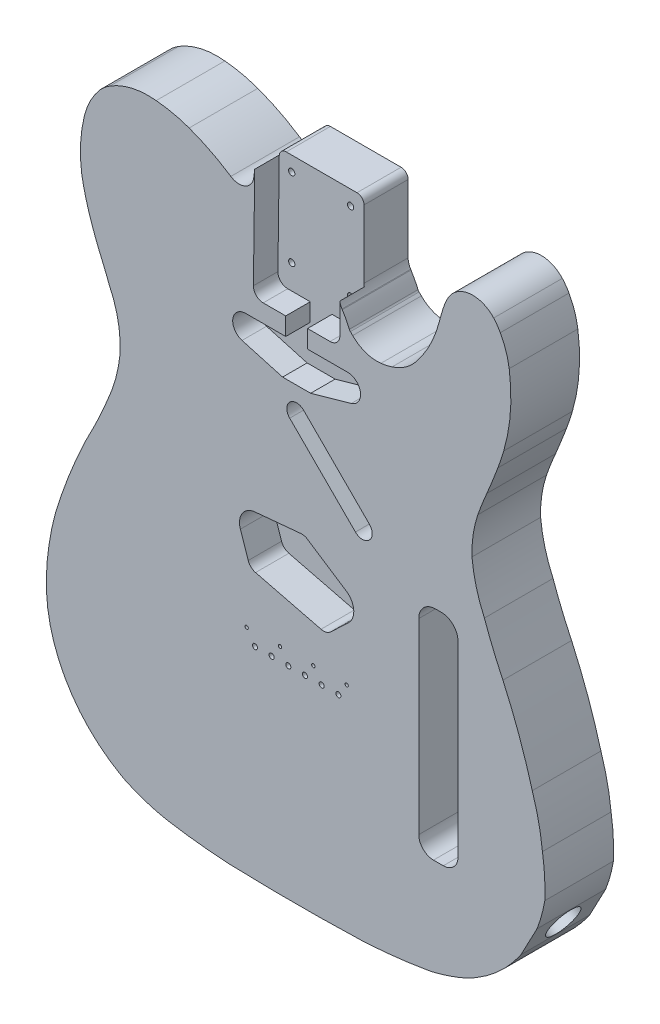
SolidWorks part; units mm, degrees
material "Teak"
ref_plane "Front Plane" through (0, 0, 0) normal (0, 0, 1) x (1, 0, 0)
ref_plane "Top Plane" through (0, 0, 0) normal (0, 1, 0) x (1, 0, 0)
ref_plane "Right Plane" through (0, 0, 0) normal (1, 0, 0) x (0, 0, -1)
sketch "Sketch1" plane through (0, 0, 0) normal (0, 0, 1) x (1, 0, 0)
  line L0 (255.3675, -212.0656) -> (264.4462, -212.0656)
  line L1 (264.4462, -212.0656) -> (273.5248, -212.0656)
  line L2 (254.4921, -211.9425) -> (229.09, -204.656)
  line L3 (274.4003, -211.9425) -> (299.8024, -204.656)
  line L4 (264.4462, -197.0288) -> (264.4462, -188.6259)
  line L5 (292.1992, -149.0184) -> (292.1992, -105.0808)
  line L6 (353.0408, -434.0524) -> (359.3908, -434.0524)
  line L7 (354.3108, -292.5744) -> (358.1208, -292.5744)
  line L8 (368.9158, -303.3694) -> (368.9158, -424.5274)
  line L9 (343.5158, -303.3694) -> (343.5158, -424.5274)
  line L10 (231.3871, -188.3166) -> (257.385, -188.3166)
  line L11 (271.5074, -188.3166) -> (297.5053, -188.3166)
  line L12 (292.2083, -154.6088) -> (292.4426, -170.3149)
  line L13 (237.3236, -111.7284) -> (236.4498, -170.3149)
  line L14 (261.2712, -222.8223) -> (261.2712, -212.0656) construction
  line L15 (267.6212, -222.5163) -> (267.6212, -212.0656) construction
  line L16 (355.5808, -417.0887) -> (440.1841, -462.3756) construction
  line L17 (409.7299, -458.6842) -> (420.0941, -439.0232)
  line L26 (233.0908, -326.0407) -> (228.0254, -311.007)
  line L27 (280.249, -340.996) -> (237.8411, -330.4226)
  line L28 (286.5004, -339.3572) -> (298.0308, -328.4613)
  line L29 (271.5011, -294.9508) -> (296.5271, -311.3952)
  line L30 (267.182, -293.874) -> (237.3652, -296.6444)
  line L31 (292.2083, -154.6088) -> (293.7952, -154.6089)
  line L32 (237.3236, -111.7284) -> (236.159, -111.7284)
  line L33 (264.4462, -533.3397) -> (264.4462, -35.9424) construction
  line L34 (264.446, -176.7596) -> (264.446, -168.3324)
  line L35 (242.7991, -176.7596) -> (257.385, -176.7596)
  line L36 (271.5074, -176.7596) -> (286.0933, -176.7596)
  line L37 (271.5074, -188.3166) -> (271.5074, -176.7596)
  line L38 (257.385, -188.3166) -> (257.385, -176.7596)
  line L39 (311.5028, -266.3979) -> (268.9363, -223.8315)
  line L40 (302.5225, -275.3781) -> (259.9561, -232.8117)
  line L41 (287.6272, -100.5088) -> (241.8598, -100.5088)
  line L42 (236.7013, -109.5293) -> (237.3226, -104.5183)
  line L45 (368.921, -411.631) -> (420.0941, -439.0232) construction
  line L46 (362.6555, -433.4859) -> (409.7299, -458.6842) construction
  line L47 (300.9797, -323.698) -> (343.5158, -323.698) construction
  line L48 (300.9797, -317.348) -> (343.5158, -317.348) construction
  line L49 (343.5158, -311.8813) -> (308.6561, -277.0216) construction
  line L50 (343.5158, -302.901) -> (313.1462, -272.5315) construction
  arc A0 (298.5861, -163.6364) -> (299.2711, -164.6283) centre (301.4937, -162.3609) ccw
  arc A1 (300.7364, -166.0922) -> (299.2711, -164.6283) centre (222.8934, -242.5472) ccw
  arc A2 (300.7364, -166.0922) -> (319.0259, -172.5122) centre (316.4123, -150.6962) ccw
  arc A3 (319.0259, -172.5122) -> (326.2352, -170.944) centre (314.4164, -133.9661) ccw
  arc A4 (326.2352, -170.944) -> (341.6924, -160.3725) centre (316.2829, -139.806) ccw
  arc A5 (341.6924, -160.3725) -> (356.9315, -129.8398) centre (280.2373, -110.6305) ccw
  arc A6 (360.2177, -118.9602) -> (356.9315, -129.8398) centre (472.2447, -158.7341) ccw
  arc A7 (363.6913, -112.2691) -> (360.2177, -118.9602) centre (386.4375, -128.3247) ccw
  arc A8 (392.0008, -110.6336) -> (363.6913, -112.2691) centre (378.4982, -122.7399) ccw
  arc A9 (396.3203, -116.7099) -> (392.0008, -110.6336) centre (367.666, -132.5065) ccw
  arc A10 (402.0691, -133.9701) -> (396.3203, -116.7099) centre (352.5181, -140.8862) ccw
  arc A11 (398.5108, -181.9349) -> (402.0691, -133.9701) centre (289.2584, -149.7157) ccw
  arc A12 (394.7117, -193.3187) -> (398.5108, -181.9349) centre (237.0194, -134.3662) ccw
  arc A13 (387.6043, -211.1738) -> (394.7117, -193.3187) centre (-23.048, -37.3677) ccw
  arc A14 (387.6043, -211.1738) -> (381.762, -226.053) centre (576.8456, -294.0659) ccw
  circle A15 centre (378.0352, -293.8788) radius 0.889
  arc A16 (425.1222, -420.753) -> (420.0941, -439.0232) centre (331.2243, -404.7385) cw
  arc A17 (380.6123, -486.1629) -> (409.7299, -458.6842) centre (333.4551, -407.0266) ccw
  arc A33 (368.9158, -303.3694) -> (358.1208, -292.5744) centre (358.1208, -303.3694) ccw
  arc A34 (354.3108, -292.5744) -> (343.5158, -303.3694) centre (354.3108, -303.3694) ccw
  arc A35 (231.3871, -188.3166) -> (229.09, -204.656) centre (231.3871, -196.6478) ccw
  arc A36 (299.8024, -204.656) -> (297.5053, -188.3166) centre (297.5053, -196.6478) ccw
  arc A37 (273.5248, -212.0656) -> (274.4003, -211.9425) centre (273.5248, -208.8906) ccw
  arc A38 (254.4921, -211.9425) -> (255.3675, -212.0656) centre (255.3675, -208.8906) ccw
  circle A39 centre (300.6412, -197.0288) radius 2.3813
  circle A40 centre (228.2512, -197.0288) radius 2.3813
  circle A41 centre (190.7346, -293.8788) radius 0.889
  circle A45 centre (216.6438, -195.7754) radius 0.9906
  circle A46 centre (237.8426, -363.958) radius 0.9906
  arc A47 (369.9797, -491.4239) -> (380.6123, -486.1629) centre (341.6053, -420.7038) ccw
  circle A49 centre (361.0363, -437.4278) radius 0.9906
  circle A50 centre (375.8404, -153.7439) radius 0.9906
  arc A51 (292.1992, -105.0808) -> (287.6272, -100.5088) centre (287.6272, -105.0808) ccw
  arc A52 (359.3908, -434.0524) -> (368.9158, -424.5274) centre (359.3908, -424.5274) ccw
  arc A53 (343.5158, -424.5274) -> (353.0408, -434.0524) centre (353.0408, -424.5274) ccw
  circle A55 centre (356.2158, -289.002) radius 0.8255
  circle A56 centre (356.2158, -437.6248) radius 0.8255
  circle A57 centre (264.4462, -249.0804) radius 1.5875
  circle A58 centre (264.4462, -477.6804) radius 1.5875
  arc A59 (286.0933, -176.7596) -> (292.4426, -170.3149) centre (286.0933, -170.4096) ccw
  arc A60 (236.4498, -170.3149) -> (242.7991, -176.7596) centre (242.7991, -170.4096) ccw
  circle A61 centre (296.8434, -363.9576) radius 1.0795
  circle A62 centre (275.2536, -363.9576) radius 1.0795
  circle A63 centre (253.664, -363.9576) radius 1.0795
  circle A64 centre (232.0734, -363.9576) radius 1.0795
  circle A65 centre (291.4462, -372.0852) radius 1.651
  circle A66 centre (280.6516, -372.0852) radius 1.651
  circle A67 centre (269.8566, -372.0852) radius 1.651
  circle A68 centre (259.061, -372.0852) radius 1.651
  circle A69 centre (248.2654, -372.0852) radius 1.651
  circle A70 centre (237.4714, -372.0852) radius 1.651
  circle A91 centre (378.3902, -122.9872) radius 0.889
  circle A92 centre (324.0598, -293.8788) radius 0.889
  circle A93 centre (228.8868, -140.5904) radius 0.889
  arc A94 (237.3652, -296.6444) -> (228.0254, -311.007) centre (238.3756, -307.5196) ccw
  arc A95 (233.0908, -326.0407) -> (237.8411, -330.4226) centre (239.4695, -323.8915) ccw
  arc A96 (280.249, -340.996) -> (286.5004, -339.3572) centre (281.8774, -334.465) ccw
  arc A97 (298.0308, -328.4613) -> (296.5271, -311.3952) centre (290.5293, -320.523) ccw
  arc A98 (271.5011, -294.9508) -> (267.182, -293.874) centre (267.8047, -300.5761) ccw
  arc A99 (268.9363, -223.8315) -> (259.9561, -232.8117) centre (264.4462, -228.3216) ccw
  arc A100 (302.5225, -275.3781) -> (311.5028, -275.3781) centre (307.0126, -270.888) ccw
  arc A101 (311.5028, -275.3781) -> (311.5028, -266.3979) centre (307.0126, -270.888) ccw
  circle A102 centre (245.3978, -160.8336) radius 2.032
  circle A103 centre (283.4978, -160.8336) radius 2.032
  circle A104 centre (283.4978, -110.0336) radius 2.032
  circle A105 centre (245.3978, -110.0336) radius 2.032
  arc A106 (241.8598, -100.5088) -> (237.3226, -104.5183) centre (241.8598, -105.0808) ccw
  arc A107 (292.1992, -149.0184) -> (293.7952, -154.6089) centre (302.5829, -149.077) ccw
  arc A108 (293.7952, -154.6089) -> (294.036, -154.9688) centre (302.7937, -148.8489) ccw
  arc A109 (298.5861, -163.6364) -> (294.036, -154.9688) centre (234.5218, -191.7393) ccw
  arc A110 (381.762, -226.053) -> (377.952, -251.638) centre (450.886, -249.4228) ccw
  arc A111 (377.952, -251.638) -> (386, -281.868) centre (472.8009, -242.5731) ccw
  arc A112 (386, -281.868) -> (398, -310.6852) centre (672.9207, -179.2964) ccw
  arc A113 (417, -363.1361) -> (398, -310.6852) centre (74.1269, -457.6731) ccw
  arc A114 (423.6009, -393.9961) -> (417, -363.1361) centre (272.0204, -410.283) ccw
  arc A115 (425.1222, -420.753) -> (423.6009, -393.9961) centre (285.4631, -415.2715) ccw
  arc A116 (353.3461, -496.801) -> (369.9797, -491.4239) centre (322.6987, -373.581) ccw
  arc A117 (307.8756, -502.3376) -> (349.8373, -497.5433) centre (288.5477, -147.1431) ccw
  arc A118 (221.4182, -502.3513) -> (307.8756, -502.3376) centre (264.4456, 766.9622) ccw
  arc A119 (182.0911, -498.0608) -> (220.5936, -502.3144) centre (240.3434, -147.16) ccw
  arc A120 (155.5294, -490.0098) -> (168.8471, -494.9386) centre (206.2073, -373.5338) ccw
  arc A121 (102.5148, -408.988) -> (150.7976, -487.651) centre (197.6727, -404.73) ccw
  arc A122 (104.046, -382.4484) -> (102.5148, -408.988) centre (242.065, -403.7256) ccw
  arc A123 (111.5356, -351.5884) -> (104.046, -382.4484) centre (255.1378, -402.7788) ccw
  arc A124 (134.1464, -299.1376) -> (111.5356, -351.5884) centre (448.2456, -465.6404) ccw
  arc A125 (134.1464, -299.1376) -> (141.8856, -281.868) centre (-139.905, -165.9555) ccw
  arc A126 (141.8856, -281.868) -> (150.1456, -251.638) centre (55.4068, -241.9953) ccw
  arc A127 (150.1456, -251.638) -> (143.0364, -216.2088) centre (77.3673, -247.8137) ccw
  arc A128 (143.0364, -216.2088) -> (136.806, -200.9676) centre (-189.4378, -343.226) ccw
  arc A129 (129.8252, -181.788) -> (136.806, -200.9676) centre (324.3166, -121.8593) ccw
  arc A130 (125.2556, -162.9888) -> (129.8252, -181.788) centre (275.6939, -136.3761) ccw
  arc A131 (127.036, -129.7188) -> (125.2556, -162.9888) centre (213.3553, -151.0206) ccw
  arc A132 (137.4456, -109.7788) -> (127.036, -129.7188) centre (173.1607, -141.1109) ccw
  arc A133 (143.666, -104.698) -> (137.4456, -109.7788) centre (162.4404, -134.0314) ccw
  arc A134 (173.5156, -97.9688) -> (143.666, -104.698) centre (168.4714, -145.1623) ccw
  arc A135 (194.8464, -102.668) -> (173.5156, -97.9688) centre (166.5725, -180.2475) ccw
  arc A136 (221.848, -116.3068) -> (194.8464, -102.668) centre (151.4563, -222.118) ccw
  arc A137 (221.848, -116.3068) -> (236.7013, -109.5293) centre (227.1904, -108.3501) ccw
  arc A138 (220.5936, -502.3144) -> (221.4182, -502.3513) centre (222.709, -464.2732) ccw
  arc A139 (349.8373, -497.5433) -> (353.3461, -496.801) centre (341.0846, -447.503) ccw
  arc A143 (168.8471, -494.9386) -> (182.0911, -498.0608) centre (198.7298, -397.8325) ccw
  arc A144 (150.7976, -487.651) -> (155.5294, -490.0098) centre (175.7968, -443.4279) ccw
  circle A145 centre (237.4714, -372.0852) radius 4.064
  circle A146 centre (248.2654, -372.0852) radius 4.064
  circle A147 centre (259.061, -372.0852) radius 4.064
  circle A148 centre (269.8566, -372.0852) radius 4.064
  circle A149 centre (280.6516, -372.0852) radius 4.064
  circle A150 centre (291.4462, -372.0852) radius 4.064
  circle A151 centre (237.4714, -372.0852) radius 4.826
  circle A152 centre (248.2654, -372.0852) radius 4.826
  circle A153 centre (259.061, -372.0852) radius 4.826
  circle A154 centre (269.8566, -372.0852) radius 4.826
  circle A155 centre (280.6516, -372.0852) radius 4.826
  circle A156 centre (291.4462, -372.0852) radius 4.826
  circle A157 centre (232.0734, -363.9576) radius 2.032
  circle A158 centre (253.664, -363.9576) radius 2.032
  circle A159 centre (275.2536, -363.9576) radius 2.032
  circle A160 centre (296.8434, -363.9576) radius 2.032
extrude "Extrude1" add sketch "Sketch1" along normal blind 44.45 contours A107 L5 A51 L41 A106 L42 A137 A136 A135 A134 A133 A132 A131 A130 A129 A128 A127 A126 A125 A124 A123 A122 A121 A144 A120 A143 A119 A138 A118 A117 A139 A116 A47 A17 L17 A16 A115 A114 A113 A112 A111 A110 A14 A13 A12 A11 A10 A9 A8 A7 A6 A5 A4 A3 A2 A1 A0 A109 A108
sketch "Sketch3" plane through (0, 0, 44.45) normal (0, 0, 1) x (1, 0, 0)
  line L17 (236.4498, -170.3149) -> (237.3226, -104.5183)
  line L18 (241.8598, -100.5088) -> (287.6272, -100.5088)
  line L203 (292.1992, -105.0808) -> (292.4426, -170.3149)
  line L204 (242.7991, -176.7596) -> (257.385, -176.7596)
  line L205 (257.385, -176.7596) -> (257.385, -188.3166)
  line L206 (257.385, -188.3166) -> (231.3871, -188.3166)
  line L207 (286.0933, -176.7596) -> (271.5074, -176.7596)
  line L208 (271.5074, -176.7596) -> (271.5074, -188.3166)
  line L209 (271.5074, -188.3166) -> (297.5053, -188.3166)
  line L210 (299.8024, -204.656) -> (273.5248, -212.0656)
  line L211 (273.5248, -212.0656) -> (255.3675, -212.0656)
  line L212 (255.3675, -212.0656) -> (229.09, -204.656)
  arc A101 (236.4498, -170.3149) -> (242.7991, -176.7596) centre (242.7991, -170.4096) ccw
  arc A102 (286.0933, -176.7596) -> (292.4426, -170.3149) centre (286.0933, -170.4096) ccw
  arc A103 (287.6272, -100.5088) -> (292.1992, -105.0808) centre (287.6272, -105.0808) cw
  arc A104 (237.3226, -104.5183) -> (241.8598, -100.5088) centre (241.8598, -105.0808) cw
  arc A105 (229.09, -204.656) -> (231.3871, -188.3166) centre (231.3871, -196.6478) cw
  arc A106 (297.5053, -188.3166) -> (299.8024, -204.656) centre (297.5053, -196.6478) cw
extrude "Cut-Extrude1" cut sketch "Sketch3" against normal blind 15.875
sketch "Sketch4" plane through (0, 0, 44.45) normal (0, 0, 1) x (1, 0, 0)
  line L1 (259.9561, -232.8117) -> (302.5225, -275.3781)
  line L2 (311.5028, -266.3979) -> (268.9363, -223.8315)
  arc A0 (259.9561, -232.8117) -> (268.9363, -223.8315) centre (264.4462, -228.3216) cw
  arc A1 (302.5225, -275.3781) -> (311.5028, -266.3979) centre (307.0126, -270.888) ccw
extrude "Cut-Extrude2" cut sketch "Sketch4" against normal blind 15.875
sketch "Sketch5" plane through (0, 0, 44.45) normal (0, 0, 1) x (1, 0, 0)
  line L0 (228.0254, -311.007) -> (233.0908, -326.0407)
  line L1 (237.8411, -330.4226) -> (280.249, -340.996)
  line L2 (286.5004, -339.3572) -> (298.0308, -328.4613)
  line L3 (296.5271, -311.3952) -> (271.5011, -294.9508)
  line L4 (267.182, -293.874) -> (237.3652, -296.6444)
  line L5 (237.3652, -296.6444) -> (237.5599, -296.573)
  arc A0 (228.0254, -311.007) -> (237.3652, -296.6444) centre (238.3756, -307.5196) cw
  arc A1 (271.5011, -294.9508) -> (267.182, -293.874) centre (267.8047, -300.5761) ccw
  arc A2 (296.5271, -311.3952) -> (298.0308, -328.4613) centre (290.5293, -320.523) cw
  arc A3 (280.249, -340.996) -> (286.5004, -339.3572) centre (281.8774, -334.465) ccw
  arc A4 (233.0908, -326.0407) -> (237.8411, -330.4226) centre (239.4695, -323.8915) ccw
extrude "Cut-Extrude3" cut sketch "Sketch5" along direction (0, 0, 1) on the side against the normal blind 21.59 contours L0 A4 L1 A3 L2 A2 L3 A1 L4 A0
sketch "Sketch6" plane through (0, 0, 44.45) normal (0, 0, 1) x (1, 0, 0)
  line L0 (354.3108, -292.5744) -> (358.1208, -292.5744)
  line L1 (368.9158, -303.3694) -> (368.9158, -424.5274)
  line L2 (359.3908, -434.0524) -> (353.0408, -434.0524)
  line L3 (343.5158, -424.5274) -> (343.5158, -303.3694)
  arc A0 (343.5158, -303.3694) -> (354.3108, -292.5744) centre (354.3108, -303.3694) cw
  arc A1 (358.1208, -292.5744) -> (368.9158, -303.3694) centre (358.1208, -303.3694) cw
  arc A2 (368.9158, -424.5274) -> (359.3908, -434.0524) centre (359.3908, -424.5274) cw
  arc A3 (353.0408, -434.0524) -> (343.5158, -424.5274) centre (353.0408, -424.5274) cw
extrude "Cut-Extrude4" cut sketch "Sketch6" against normal blind 38.1
sketch "Sketch7" plane through (0, 0, 44.45) normal (0, 0, 1) x (1, 0, 0)
  circle A0 centre (245.3978, -110.0336) radius 2.032
  circle A1 centre (283.4978, -110.0336) radius 2.032
  circle A2 centre (283.4978, -160.8336) radius 2.032
  circle A3 centre (245.3978, -160.8336) radius 2.032
  circle A4 centre (237.4714, -372.0852) radius 1.651
  circle A5 centre (248.2654, -372.0852) radius 1.651
  circle A6 centre (259.061, -372.0852) radius 1.651
  circle A7 centre (269.8566, -372.0852) radius 1.651
  circle A8 centre (280.6516, -372.0852) radius 1.651
  circle A9 centre (291.4462, -372.0852) radius 1.651
  circle A10 centre (296.8434, -363.9576) radius 1.0795
  circle A11 centre (275.2536, -363.9576) radius 1.0795
  circle A12 centre (232.0734, -363.9576) radius 1.0795
  circle A13 centre (253.664, -363.9576) radius 1.0795
extrude "Cut-Extrude5" cut sketch "Sketch7" against normal through all
sketch "Sketch9" plane through (509.8461, -268.762, 0) normal (0.8846, -0.4663, 0) x (0, 0, -1)
  circle A0 centre (-22.225, -203.708) radius 10.4775
extrude "Cut-Extrude6" cut sketch "Sketch9" against normal blind 60.96
